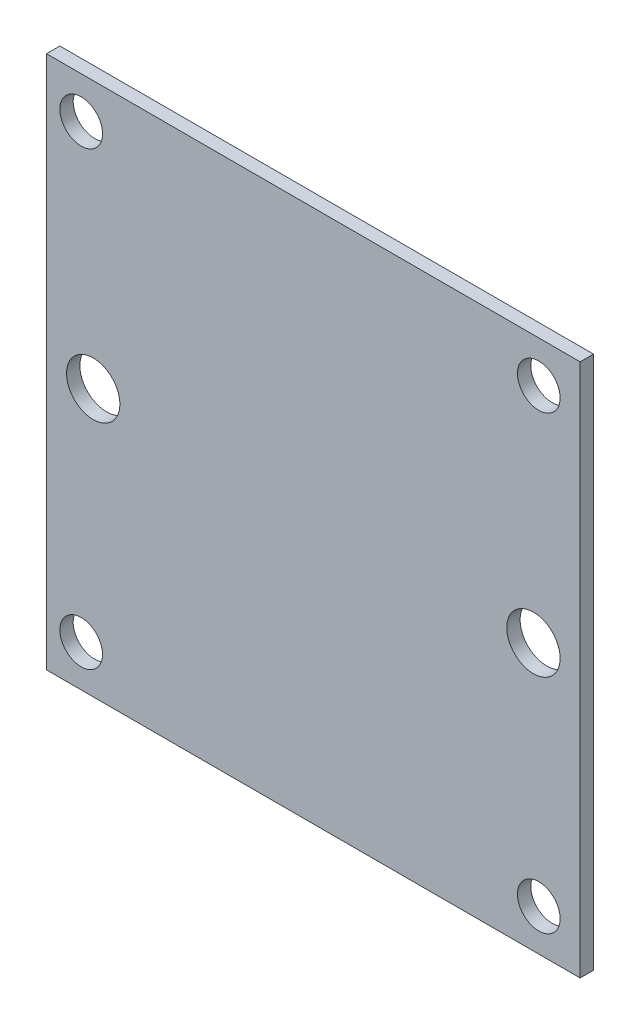
SolidWorks part; units mm, degrees
ref_plane "Front Plane" through (0, 0, 0) normal (0, 0, 1) x (1, 0, 0)
ref_plane "Top Plane" through (0, 0, 0) normal (0, 1, 0) x (1, 0, 0)
ref_plane "Right Plane" through (0, 0, 0) normal (1, 0, 0) x (0, 0, -1)
sketch "Sketch1" plane through (0, 0, 0) normal (0, 0, 1) x (1, 0, 0)
  line L1 (-20, 20) -> (20, 20)
  line L2 (-20, 20) -> (-20, -20)
  line L3 (-20, -20) -> (20, -20)
  line L4 (20, 20) -> (20, -20)
  line L5 (-20, 20) -> (20, -20) construction
  line L6 (-20, -20) -> (20, 20) construction
  point P0 (0, 0)
  dimension "D1" = 40
  dimension "D2" = 40
extrude "Boss-Extrude1" add sketch "Sketch1" along normal blind 1
sketch "Sketch2" plane through (0, 0, 1) normal (0, 0, 1) x (1, 0, 0)
  line L0 (-20, 20) -> (-20, -20) construction
  line L1 (20, 20) -> (-20, 20) construction
  line L2 (20, -20) -> (20, 20) construction
  line L3 (-20, -20) -> (20, -20) construction
  circle A0 centre (-17.4, -16.9) radius 1.6
  circle A1 centre (16.9, -16.9) radius 1.6
  circle A2 centre (16.9, 16.9) radius 1.6
  circle A3 centre (-17.4, 16.9) radius 1.6
  circle A5 centre (16.5, 0) radius 2
  circle A7 centre (-16.5, 0) radius 2
  dimension "D1" = 3.5
  dimension "D5" = 3.1
  dimension "D6" = 20
  dimension "D2" = 3.1
  dimension "D3" = 3.5
  dimension "D4" = 3.1
extrude "Cut-Extrude1" cut sketch "Sketch2" against normal blind 10
